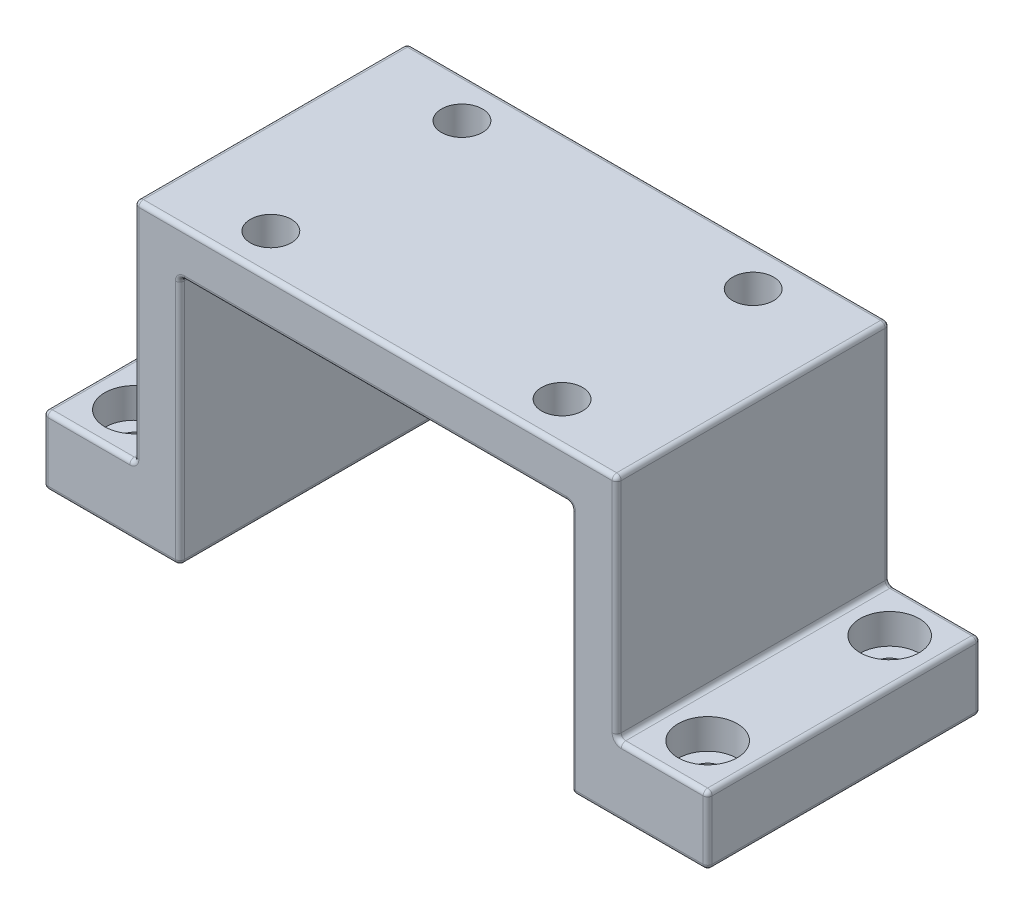
SolidWorks part; units mm, degrees
material "1.0045 (S355JR)"
ref_plane "Front Plane" through (0, 0, 0) normal (0, 0, 1) x (1, 0, 0)
ref_plane "Top Plane" through (0, 0, 0) normal (0, 1, 0) x (1, 0, 0)
ref_plane "Right Plane" through (0, 0, 0) normal (1, 0, 0) x (0, 0, -1)
sketch "Sketch1" plane through (0, 0, 0) normal (0, 1, 0) x (1, 0, 0)
  line L1 (-53, -30) -> (53, -30)
  line L2 (-53, -30) -> (-53, 30)
  line L3 (-53, 30) -> (53, 30)
  line L4 (53, -30) -> (53, 30)
  line L5 (-53, -30) -> (53, 30) construction
  line L6 (-53, 30) -> (53, -30) construction
  point P0 (0, 0)
  dimension "D1" = 60
  dimension "D2" = 106
extrude "Boss-Extrude1" add sketch "Sketch1" along normal blind 10
sketch "Sketch2" plane through (0, 0, 0) normal (0, -1, 0) x (1, 0, 0)
  line L0 (53, -30) -> (-53, -30) construction
  line L1 (-53, 30) -> (-43, 30)
  line L2 (-53, 30) -> (-53, -30)
  line L3 (-53, -30) -> (-43, -30)
  line L4 (-43, 30) -> (-43, -30)
  line L6 (53, 30) -> (43, 30)
  line L7 (53, 30) -> (53, -30)
  line L8 (53, -30) -> (43, -30)
  line L9 (43, 30) -> (43, -30)
  dimension "D1" = 10
  dimension "D2" = 10
extrude "Boss-Extrude2" add sketch "Sketch2" along normal blind 55
sketch "Sketch3" plane through (53, 0, 0) normal (1, 0, 0) x (0, 0, -1)
  line L0 (30, 10) -> (30, -55) construction
  line L1 (-30, -55) -> (30, -55)
  line L2 (-30, -55) -> (-30, -40)
  line L3 (-30, -40) -> (30, -40)
  line L4 (30, -55) -> (30, -40)
  dimension "D1" = 15
extrude "Boss-Extrude3" add sketch "Sketch3" along normal blind 20
sketch "Sketch4" plane through (-53, 0, 0) normal (-1, 0, 0) x (0, 0, 1)
  line L0 (30, 10) -> (30, -55) construction
  line L1 (-30, -55) -> (30, -55)
  line L2 (-30, -55) -> (-30, -40)
  line L3 (-30, -40) -> (30, -40)
  line L4 (30, -55) -> (30, -40)
  dimension "D1" = 15
extrude "Boss-Extrude4" add sketch "Sketch4" along normal blind 20
sketch "Sketch5" plane through (0, 10, 0) normal (0, 1, 0) x (1, 0, 0)
  line L0 (0, 0) -> (0, 30) construction
  line L1 (53, 30) -> (-53, 30) construction
  line L2 (0, 0) -> (18.8591, 0) construction
  circle A0 centre (-32, 21) radius 4.5
  circle A1 centre (32, 21) radius 4.5
  circle A2 centre (32, -21) radius 4.5
  circle A3 centre (-32, -21) radius 4.5
  dimension "D3" = 9
  dimension "D1" = 32
  dimension "D2" = 21
extrude "Cut-Extrude1" cut sketch "Sketch5" against normal through all
sketch "Sketch6" plane through (0, -40, 0) normal (0, 1, 0) x (1, 0, 0)
  line L0 (73, 30) -> (53, 30) construction
  line L1 (73, 30) -> (73, -30) construction
  line L2 (73, -30) -> (53, -30) construction
  line L3 (-73, -30) -> (-73, 30) construction
  line L4 (-73, 30) -> (-53, 30) construction
  line L5 (-73, -30) -> (-53, -30) construction
  circle A0 centre (63, 20) radius 6.5
  circle A1 centre (63, -20) radius 6.5
  circle A2 centre (-63, 20) radius 6.5
  circle A3 centre (-63, -20) radius 6.5
  dimension "D2" = 10
  dimension "D9" = 13
  dimension "D10" = 13
  dimension "D11" = 13
  dimension "D12" = 13
  dimension "D1" = 10
  dimension "D3" = 10
  dimension "D4" = 10
  dimension "D5" = 10
  dimension "D6" = 10
  dimension "D7" = 10
  dimension "D8" = 10
extrude "Cut-Extrude2" cut sketch "Sketch6" against normal blind 6.6
sketch "Sketch7" plane through (0, -46.6, 0) normal (0, 1, 0) x (1, 0, 0)
  circle A0 centre (-63, 20) radius 3.3
  circle A1 centre (-63, -20) radius 3.3
  circle A2 centre (63, -20) radius 3.3
  circle A3 centre (63, 20) radius 3.3
  dimension "D1" = 6.6
  dimension "D2" = 6.6
  dimension "D3" = 6.6
  dimension "D4" = 6.6
extrude "Cut-Extrude3" cut sketch "Sketch7" against normal through all
fillet "Fillet1" radius 1 36 edges at (43, -27.5, -30) (-43, -27.5, -30) (-43, -27.5, 30) (43, -27.5, 30) (0, 0, -30) (0, 0, 30) (-43, 0, 0) (43, 0, 0) (53, -15, -30) (-53, -15, -30) (53, -15, 30) (-53, -15, 30) (53, 10, 0) (0, 10, -30) (-53, 10, 0) (0, 10, 30) (63, -40, 30) (-63, -40, 30) (-63, -40, -30) (58, -55, 30) (73, -47.5, 30) (53, -40, 0) (63, -40, -30) (73, -40, 0) (73, -55, 0) (73, -47.5, -30) (58, -55, -30) (-43, -55, 0) (43, -55, 0) (-58, -55, -30) (-73, -47.5, -30) (-73, -55, 0) (-58, -55, 30) (-73, -47.5, 30) (-73, -40, 0) (-53, -40, 0)
